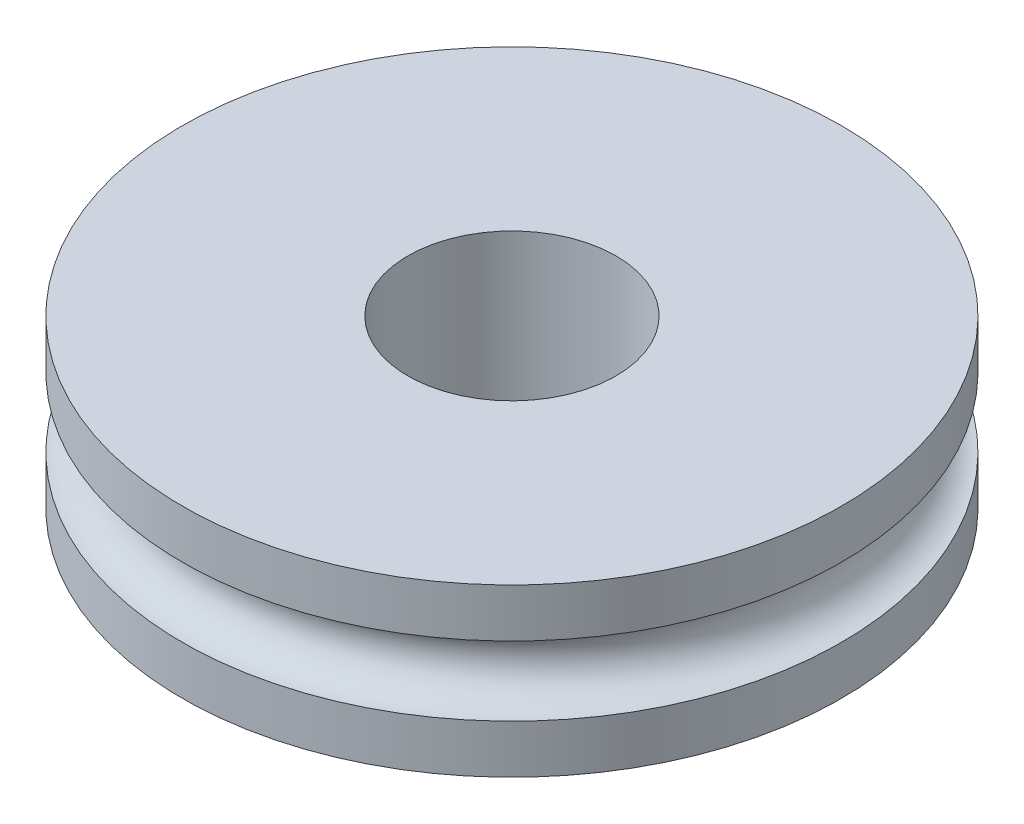
SolidWorks part; units mm, degrees
material "ABS"
ref_plane "Front Plane" through (0, 0, 0) normal (0, 0, 1) x (1, 0, 0)
ref_plane "Top Plane" through (0, 0, 0) normal (0, 1, 0) x (1, 0, 0)
ref_plane "Right Plane" through (0, 0, 0) normal (1, 0, 0) x (0, 0, -1)
sketch "Sketch1" plane through (0, 0, 0) normal (0, 0, 1) x (1, 0, 0)
  line L0 (0, 0) -> (0, 5.0186) construction
  line L1 (0, 0) -> (4.75, 0) construction
  line L2 (1.5, -1.2) -> (1.5, 1.2)
  line L3 (1.5, 1.2) -> (4.75, 1.2)
  line L4 (4.75, 1.2) -> (4.75, 0.5)
  line L5 (4.75, -1.2) -> (4.75, -0.5)
  line L6 (1.5, -1.2) -> (4.75, -1.2)
  arc A0 (4.75, 0.5) -> (4.75, -0.5) centre (4.75, 0) ccw
  point P11 (1.5, 0)
  dimension "D1" = 4.75
  dimension "D2" = 0.7
  dimension "D3" = 1.5
  dimension "D4" = 1.2
revolve "Revolve1" add sketch "Sketch1" angle 360 about L0
